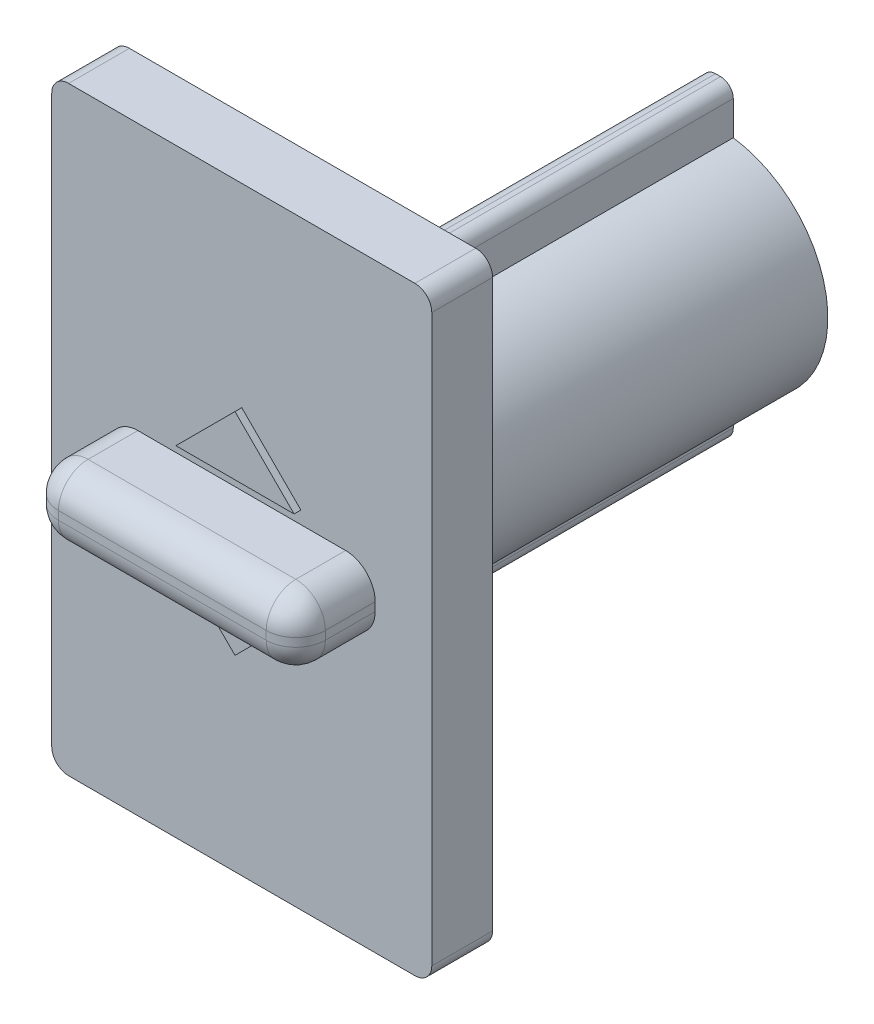
SolidWorks part; units mm, degrees
ref_plane "Front Plane" through (0, 0, 0) normal (1, 0, 0) x (0, 1, 0)
ref_plane "Top Plane" through (0, 0, 0) normal (0, 0, 1) x (0, 1, 0)
ref_plane "Right Plane" through (0, 0, 0) normal (0, 1, 0) x (-1, 0, 0)
sketch "Sketch1" plane through (0, 0, 0) normal (0, 0, 1) x (0, 1, 0)
  line L0 (0, 0) -> (17.75, 0) construction
  line L1 (17.75, 0) -> (17.75, 11.25) construction
  line L3 (-17.75, -11.25) -> (17.75, -11.25)
  line L4 (-17.75, -11.25) -> (-17.75, 11.25)
  line L5 (-17.75, 11.25) -> (17.75, 11.25)
  line L6 (17.75, -11.25) -> (17.75, 11.25)
  line L7 (-17.75, -11.25) -> (17.75, 11.25) construction
  line L8 (-17.75, 11.25) -> (17.75, -11.25) construction
extrude "Boss-Extrude1" add sketch "Sketch1" along normal blind 3.6
sketch "Sketch2" plane through (0, 0, 3.6) normal (0, 0, 1) x (1, 0, 0)
  line L0 (0, 0) -> (0, 2) construction
  line L1 (0, 2) -> (7.9, 2) construction
  line L3 (-7.9, -2) -> (7.9, -2)
  line L4 (-7.9, -2) -> (-7.9, 2)
  line L5 (-7.9, 2) -> (7.9, 2)
  line L6 (7.9, -2) -> (7.9, 2)
  line L7 (-7.9, -2) -> (7.9, 2) construction
  line L8 (-7.9, 2) -> (7.9, -2) construction
extrude "Boss-Extrude2" add sketch "Sketch2" along normal blind 4.7
sketch "Sketch3" plane through (0, 0, 0) normal (0, 0, -1) x (1, 0, 0)
  circle A1 centre (0, 0) radius 6.5
extrude "Boss-Extrude3" add sketch "Sketch3" along normal blind 24.6
sketch "Sketch4" plane through (0, 0, -24.6) normal (0, 0, -1) x (1, 0, 0)
  line L0 (0, 0) -> (3, 0) construction
  line L1 (3, 0) -> (3, 3.75) construction
  line L3 (-3, -3.75) -> (3, -3.75)
  line L4 (-3, -3.75) -> (-3, 3.75)
  line L5 (-3, 3.75) -> (3, 3.75)
  line L6 (3, -3.75) -> (3, 3.75)
  line L7 (-3, -3.75) -> (3, 3.75) construction
  line L8 (-3, 3.75) -> (3, -3.75) construction
extrude "Cut-Extrude1" cut sketch "Sketch4" against normal blind 16
sketch "Sketch5" plane through (0, 0, -24.6) normal (0, 0, -1) x (-1, 0, 0)
  line L0 (0, 0) -> (0, -3.75) construction
  line L1 (-3, -3.75) -> (3, -3.75) construction
  line L2 (0, 0) -> (0, 3.75) construction
  line L3 (3, 3.75) -> (-3, 3.75) construction
  line L4 (0, 0) -> (-3, 0) construction
  line L5 (-3, 3.75) -> (-3, -3.75) construction
  line L6 (0, 0) -> (3, 0) construction
  line L7 (3, -3.75) -> (3, 3.75) construction
  line L9 (-0.5, 3.95) -> (0.5, 3.95)
  line L10 (-0.5, 3.95) -> (-0.5, 3.55)
  line L11 (-0.5, 3.55) -> (0.5, 3.55)
  line L12 (0.5, 3.95) -> (0.5, 3.55)
  line L13 (-0.5, 3.95) -> (0.5, 3.55) construction
  line L14 (-0.5, 3.55) -> (0.5, 3.95) construction
  line L15 (-3.2, 0.5) -> (-2.8, 0.5)
  line L16 (-3.2, 0.5) -> (-3.2, -0.5)
  line L17 (-3.2, -0.5) -> (-2.8, -0.5)
  line L18 (-2.8, 0.5) -> (-2.8, -0.5)
  line L19 (-3.2, 0.5) -> (-2.8, -0.5) construction
  line L20 (-3.2, -0.5) -> (-2.8, 0.5) construction
  line L21 (-0.5, -3.95) -> (0.5, -3.95)
  line L22 (-0.5, -3.95) -> (-0.5, -3.55)
  line L23 (-0.5, -3.55) -> (0.5, -3.55)
  line L24 (0.5, -3.95) -> (0.5, -3.55)
  line L25 (-0.5, -3.95) -> (0.5, -3.55) construction
  line L26 (-0.5, -3.55) -> (0.5, -3.95) construction
  line L27 (2.8, 0.5) -> (3.2, 0.5)
  line L28 (2.8, 0.5) -> (2.8, -0.5)
  line L29 (2.8, -0.5) -> (3.2, -0.5)
  line L30 (3.2, 0.5) -> (3.2, -0.5)
  line L31 (2.8, 0.5) -> (3.2, -0.5) construction
  line L32 (2.8, -0.5) -> (3.2, 0.5) construction
  dimension "D1" = 1
  dimension "D2" = 0.4
  dimension "D3" = 1
  dimension "D4" = 1
  dimension "D5" = 1
  dimension "D6" = 0.4
  dimension "D7" = 0.4
  dimension "D8" = 0.4
extrude "Boss-Extrude4" add sketch "Sketch5" against normal blind 16
fillet "Fillet1" radius 1 4 edges at (11.25, 17.75, 1.8) (11.25, -17.75, 1.8) (-11.25, -17.75, 1.8) (-11.25, 17.75, 1.8)
fillet "Fillet2" radius 1.75 8 edges at (7.9, -2, 5.95) (-7.9, 2, 5.95) (-7.9, -2, 5.95) (-7.9, 0, 8.3) (0, -2, 8.3) (7.9, 0, 8.3) (0, 2, 8.3) (7.9, 2, 5.95)
sketch "Sketch6" plane through (0, 0, 3.6) normal (0, 0, 1) x (1, 0, 0)
  line L0 (0, 0) -> (0, 6.25) construction
  line L1 (0, 0) -> (0, -6.25) construction
  line L2 (0, 6.25) -> (3.5, 6.25) construction
  line L3 (3.5, 6.25) -> (3.5, 2.75) construction
  line L4 (0, -6.25) -> (3.5, -6.25) construction
  line L5 (3.5, -6.25) -> (3.5, -2.75) construction
  line L6 (3.5, 2.75) -> (-3.5, 2.75)
  line L7 (-3.5, 2.75) -> (0, 6.25)
  line L8 (0, 6.25) -> (3.5, 2.75)
  line L9 (3.5, -2.75) -> (-3.5, -2.75)
  line L10 (-3.5, -2.75) -> (0, -6.25)
  line L11 (0, -6.25) -> (3.5, -2.75)
extrude "Boss-Extrude5" add sketch "Sketch6" along normal blind 0.4
sketch "Sketch7" plane through (0, 0, -24.6) normal (0, 0, -1) x (1, 0, 0)
  line L0 (0, 0) -> (0, 9.2) construction
  line L1 (0, 0) -> (0, -9.2) construction
  line L3 (-0.9, 3.8) -> (0.9, 3.8)
  line L4 (-0.9, 3.8) -> (-0.9, 9.2)
  line L5 (-0.9, 9.2) -> (0.9, 9.2)
  line L6 (0.9, 3.8) -> (0.9, 9.2)
  line L7 (-0.9, 3.8) -> (0.9, 9.2) construction
  line L8 (-0.9, 9.2) -> (0.9, 3.8) construction
  line L9 (-0.9, -3.8) -> (0.9, -3.8)
  line L10 (-0.9, -3.8) -> (-0.9, -9.2)
  line L11 (-0.9, -9.2) -> (0.9, -9.2)
  line L12 (0.9, -3.8) -> (0.9, -9.2)
  line L13 (-0.9, -3.8) -> (0.9, -9.2) construction
  line L14 (-0.9, -9.2) -> (0.9, -3.8) construction
  circle A0 centre (0, 0) radius 6.5 construction
  point P3 (0, 6.5)
  point P11 (0, -6.5)
  dimension "D1" = 1.8
  dimension "D2" = 1.8
extrude "Boss-Extrude6" add sketch "Sketch7" against normal blind 26
fillet "Fillet3" radius 0.75 4 edges at (-0.9, 9.2, -12.3) (0.9, 9.2, -12.3) (0.9, -9.2, -12.3) (-0.9, -9.2, -12.3)
